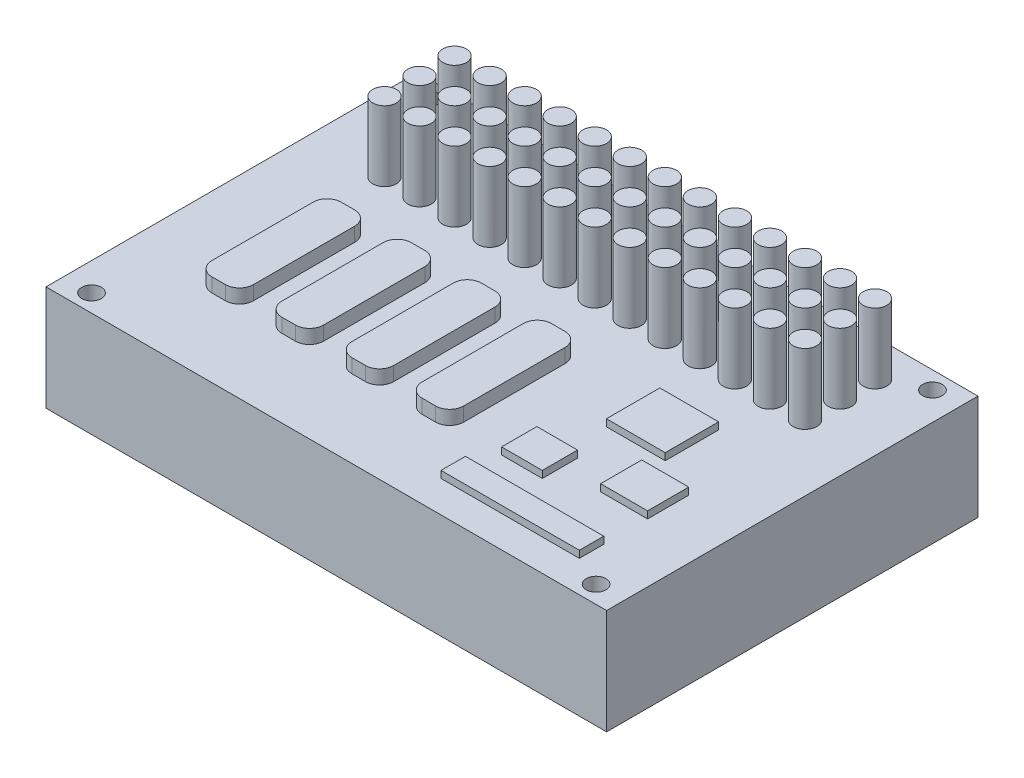
SolidWorks part; units mm, degrees
ref_plane "前视基准面" through (0, 0, 0) normal (0, 0, 1) x (1, 0, 0)
ref_plane "上视基准面" through (0, 0, 0) normal (0, 1, 0) x (1, 0, 0)
ref_plane "右视基准面" through (0, 0, 0) normal (1, 0, 0) x (0, 0, -1)
sketch "草图1" plane through (0, 0, 0) normal (0, 1, 0) x (1, 0, 0)
  line L0 (80, 53) -> (80, 0)
  line L1 (0, 0) -> (0, 53)
  line L2 (0, 53) -> (39.5, 53)
  line L3 (41.5, 53) -> (80, 53)
  line L4 (0, 0) -> (80, 0)
  line L5 (39.5, 53) -> (41.5, 53)
  circle A0 centre (76, 50.5) radius 1.4
  circle A1 centre (76, 2.5) radius 1.4
  circle A2 centre (4, 50.5) radius 1.4
  circle A3 centre (4, 2.5) radius 1.4
extrude "凸台-拉伸1" add sketch "草图1" along normal blind 15
sketch "草图2" plane through (0, 15, 0) normal (0, 1, 0) x (1, 0, 0)
  circle A0 centre (10.5869, 47.7213) radius 1.682
  circle A1 centre (15.5869, 47.7213) radius 1.682
  circle A2 centre (20.5869, 47.7213) radius 1.682
  circle A3 centre (25.5869, 47.7213) radius 1.682
  circle A4 centre (30.5869, 47.7213) radius 1.682
  circle A5 centre (35.5869, 47.7213) radius 1.682
  circle A6 centre (40.5869, 47.7213) radius 1.682
  circle A7 centre (45.5869, 47.7213) radius 1.682
  circle A8 centre (50.5869, 47.7213) radius 1.682
  circle A9 centre (55.5869, 47.7213) radius 1.682
  circle A10 centre (60.5869, 47.7213) radius 1.682
  circle A11 centre (65.5869, 47.7213) radius 1.682
  circle A12 centre (70.5869, 47.7213) radius 1.682
  circle A13 centre (15.5869, 42.7213) radius 1.682
  circle A14 centre (20.5869, 42.7213) radius 1.682
  circle A15 centre (25.5869, 42.7213) radius 1.682
  circle A16 centre (30.5869, 42.7213) radius 1.682
  circle A17 centre (35.5869, 42.7213) radius 1.682
  circle A18 centre (40.5869, 42.7213) radius 1.682
  circle A19 centre (45.5869, 42.7213) radius 1.682
  circle A20 centre (50.5869, 42.7213) radius 1.682
  circle A21 centre (55.5869, 42.7213) radius 1.682
  circle A22 centre (60.5869, 42.7213) radius 1.682
  circle A23 centre (65.5869, 42.7213) radius 1.682
  circle A24 centre (70.5869, 42.7213) radius 1.682
  circle A25 centre (15.5869, 37.7213) radius 1.682
  circle A26 centre (20.5869, 37.7213) radius 1.682
  circle A27 centre (25.5869, 37.7213) radius 1.682
  circle A28 centre (30.5869, 37.7213) radius 1.682
  circle A29 centre (35.5869, 37.7213) radius 1.682
  circle A30 centre (40.5869, 37.7213) radius 1.682
  circle A31 centre (45.5869, 37.7213) radius 1.682
  circle A32 centre (50.5869, 37.7213) radius 1.682
  circle A33 centre (55.5869, 37.7213) radius 1.682
  circle A34 centre (60.5869, 37.7213) radius 1.682
  circle A35 centre (65.5869, 37.7213) radius 1.682
  circle A36 centre (70.5869, 37.7213) radius 1.682
  circle A37 centre (10.5869, 42.7213) radius 1.682
  circle A38 centre (10.5869, 37.7213) radius 1.682
  dimension "D1" = 13
  dimension "D2" = 3
extrude "凸台-拉伸2" add sketch "草图2" along normal blind 10
sketch "草图3" plane through (0, 15, 0) normal (0, 1, 0) x (1, 0, 0)
  line L0 (20.5869, 27.5316) -> (20.5869, 13.0839)
  line L1 (12.5869, 29.5316) -> (14.5211, 29.5316)
  line L2 (10.5869, 27.5316) -> (10.5869, 13.0839)
  line L3 (12.5869, 11.0839) -> (14.5211, 11.0839)
  line L4 (16.5211, 27.5316) -> (16.5211, 13.0839)
  line L5 (26.5211, 27.5316) -> (26.5211, 13.0839)
  line L6 (22.5869, 11.0839) -> (24.5211, 11.0839)
  line L7 (22.5869, 29.5316) -> (24.5211, 29.5316)
  line L8 (30.5869, 27.5316) -> (30.5869, 13.0839)
  line L9 (36.5211, 27.5316) -> (36.5211, 13.0839)
  line L10 (32.5869, 11.0839) -> (34.5211, 11.0839)
  line L11 (32.5869, 29.5316) -> (34.5211, 29.5316)
  line L12 (40.5869, 27.5316) -> (40.5869, 13.0839)
  line L13 (46.5211, 27.5316) -> (46.5211, 13.0839)
  line L14 (42.5869, 11.0839) -> (44.5211, 11.0839)
  line L15 (42.5869, 29.5316) -> (44.5211, 29.5316)
  arc A0 (10.5869, 13.0839) -> (12.5869, 11.0839) centre (12.5869, 13.0839) ccw
  arc A1 (14.5211, 11.0839) -> (16.5211, 13.0839) centre (14.5211, 13.0839) ccw
  arc A2 (16.5211, 27.5316) -> (14.5211, 29.5316) centre (14.5211, 27.5316) ccw
  arc A3 (12.5869, 29.5316) -> (10.5869, 27.5316) centre (12.5869, 27.5316) ccw
  arc A4 (24.5211, 11.0839) -> (26.5211, 13.0839) centre (24.5211, 13.0839) ccw
  arc A5 (20.5869, 13.0839) -> (22.5869, 11.0839) centre (22.5869, 13.0839) ccw
  arc A6 (22.5869, 29.5316) -> (20.5869, 27.5316) centre (22.5869, 27.5316) ccw
  arc A7 (26.5211, 27.5316) -> (24.5211, 29.5316) centre (24.5211, 27.5316) ccw
  arc A8 (34.5211, 11.0839) -> (36.5211, 13.0839) centre (34.5211, 13.0839) ccw
  arc A9 (30.5869, 13.0839) -> (32.5869, 11.0839) centre (32.5869, 13.0839) ccw
  arc A10 (32.5869, 29.5316) -> (30.5869, 27.5316) centre (32.5869, 27.5316) ccw
  arc A11 (36.5211, 27.5316) -> (34.5211, 29.5316) centre (34.5211, 27.5316) ccw
  arc A12 (44.5211, 11.0839) -> (46.5211, 13.0839) centre (44.5211, 13.0839) ccw
  arc A13 (40.5869, 13.0839) -> (42.5869, 11.0839) centre (42.5869, 13.0839) ccw
  arc A14 (42.5869, 29.5316) -> (40.5869, 27.5316) centre (42.5869, 27.5316) ccw
  arc A15 (46.5211, 27.5316) -> (44.5211, 29.5316) centre (44.5211, 27.5316) ccw
  dimension "D1" = 2
  dimension "D2" = 4
extrude "凸台-拉伸3" add sketch "草图3" along normal blind 2
sketch "草图4" plane through (0, 15, 0) normal (0, 1, 0) x (1, 0, 0)
  line L1 (57.2867, 30.3056) -> (65.672, 30.3056)
  line L2 (57.2867, 30.3056) -> (57.2867, 22.6944)
  line L3 (57.2867, 22.6944) -> (65.672, 22.6944)
  line L4 (65.672, 30.3056) -> (65.672, 22.6944)
  line L5 (53.2875, 16.7601) -> (59.0927, 16.7601)
  line L6 (53.2875, 16.7601) -> (53.2875, 11.7289)
  line L7 (53.2875, 11.7289) -> (59.0927, 11.7289)
  line L8 (59.0927, 16.7601) -> (59.0927, 11.7289)
  line L9 (64.8979, 20.1143) -> (71.6062, 20.1143)
  line L10 (64.8979, 20.1143) -> (64.8979, 14.2445)
  line L11 (64.8979, 14.2445) -> (71.6062, 14.2445)
  line L12 (71.6062, 20.1143) -> (71.6062, 14.2445)
  line L13 (51.8684, 7.9878) -> (71.6062, 7.9878)
  line L14 (51.8684, 7.9878) -> (51.8684, 4.5047)
  line L15 (51.8684, 4.5047) -> (71.6062, 4.5047)
  line L16 (71.6062, 7.9878) -> (71.6062, 4.5047)
extrude "凸台-拉伸4" add sketch "草图4" along normal blind 1
